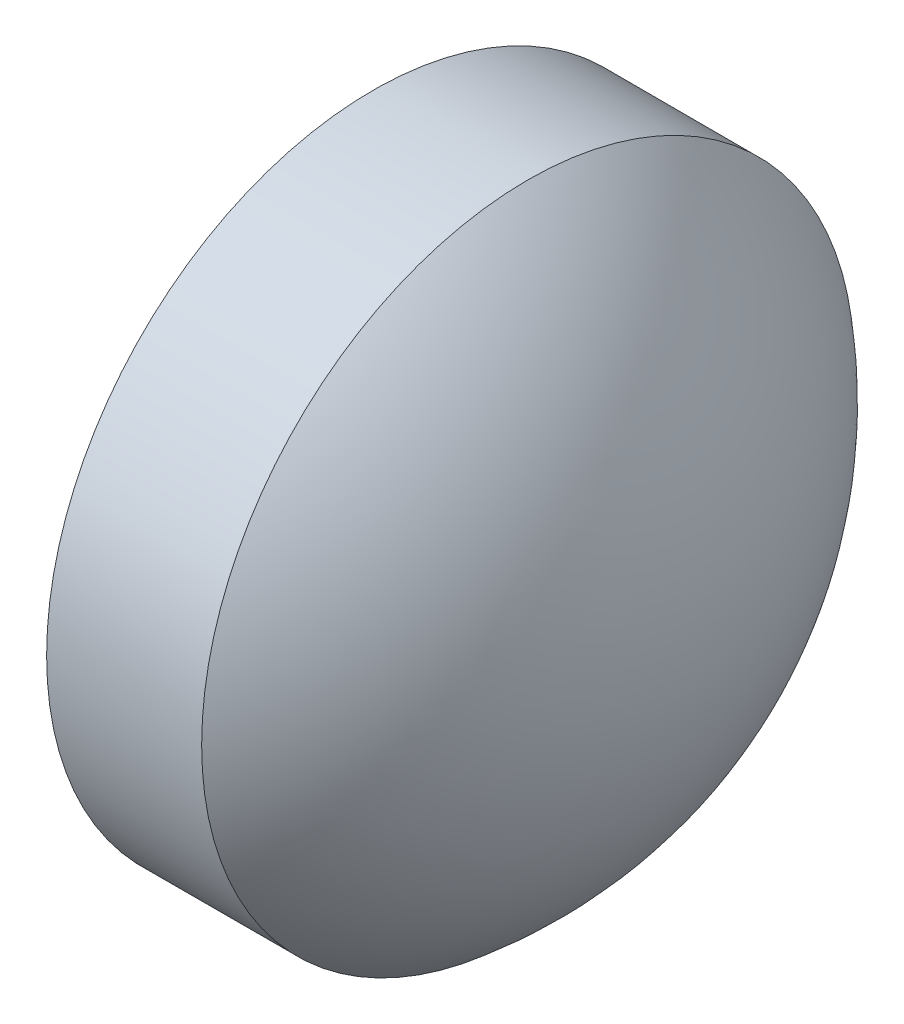
SolidWorks part; units mm, degrees
ref_plane "前视基准面" through (0, 0, 0) normal (0, 0, 1) x (1, 0, 0)
ref_plane "上视基准面" through (0, 0, 0) normal (0, 1, 0) x (1, 0, 0)
ref_plane "右视基准面" through (0, 0, 0) normal (1, 0, 0) x (0, 0, -1)
sketch "草图1" plane through (0, 0, 0) normal (0, 0, 1) x (1, 0, 0)
  line L0 (386.7687, 29.3681) -> (389.8364, 29.3681) construction
  line L1 (387.116, 29.3681) -> (387.116, 31.3681)
  line L2 (387.116, 31.3681) -> (388.066, 31.3681)
  line L3 (389.016, 29.3681) -> (387.116, 29.3681)
  arc A0 (389.016, 29.3681) -> (388.066, 31.3681) centre (386.4357, 29.3681) ccw
revolve "旋转1" add sketch "草图1" angle 360 about L0
